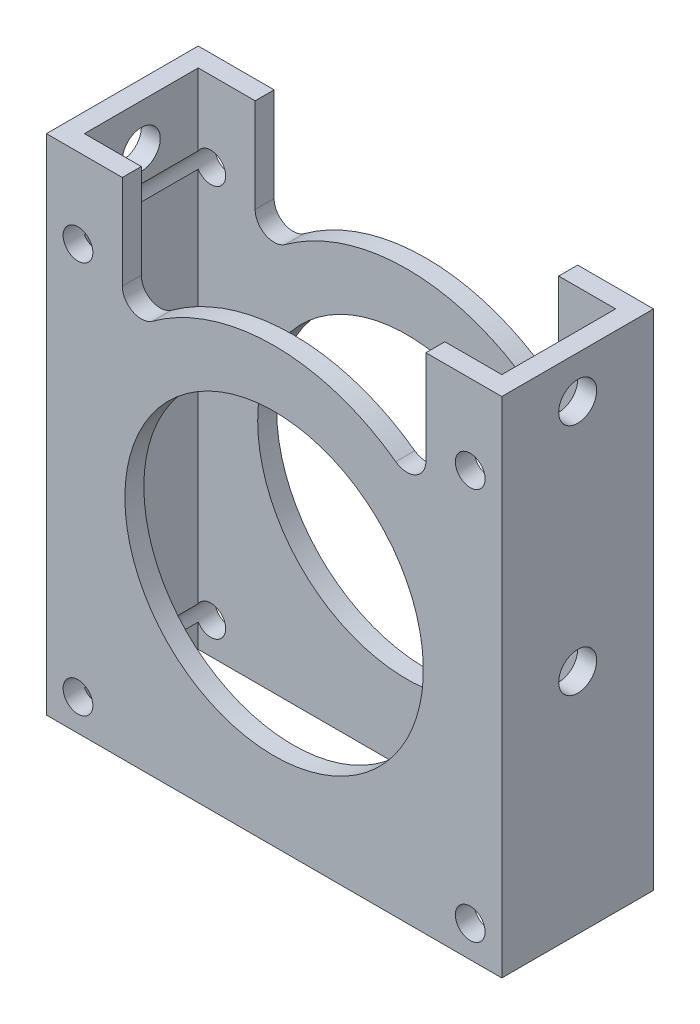
SolidWorks part; units mm, degrees
ref_plane "Front Plane" through (0, 0, 0) normal (0, 0, 1) x (1, 0, 0)
ref_plane "Top Plane" through (0, 0, 0) normal (0, 1, 0) x (1, 0, 0)
ref_plane "Right Plane" through (0, 0, 0) normal (1, 0, 0) x (0, 0, -1)
sketch "Sketch1" plane through (0, 0, 0) normal (0, 1, 0) x (1, 0, 0)
  line L1 (0, 0) -> (76.2, 0)
  line L2 (0, 0) -> (0, 25.4)
  line L3 (0, 25.4) -> (76.2, 25.4)
  line L4 (76.2, 0) -> (76.2, 25.4)
  dimension "D1" = 76.2
  dimension "D2" = 25.4
extrude "Extrude-Thin1" add sketch "Sketch1" along normal mid plane 98.552 thin thin type one direction reverse wall 3.175
sketch "Sketch2" plane through (0, 0, -25.4) normal (0, 0, -1) x (-1, 0, 0)
  line L7 (0, -49.276) -> (-76.2, 26.924) construction
  line L8 (-76.2, 49.276) -> (-76.2, -49.276) construction
  line L9 (0, 49.276) -> (0, -49.276) construction
  line L10 (-76.2, -49.276) -> (0, 26.924) construction
  circle A0 centre (-5.2832, 21.6408) radius 2.4892
  circle A2 centre (-38.1, -11.176) radius 24.972
  circle A3 centre (-70.9168, -43.9928) radius 2.4892
  point P14 (-2.794, 21.6408)
  point P17 (-73.406, -43.9928)
  dimension "D1" = 2.794
  dimension "D2" = 4.9784
  dimension "D3" = 49.944
  dimension "D4" = 2.794
extrude "Cut-Extrude1" cut sketch "Sketch2" against normal blind 52.578
sketch "Sketch5" plane through (0, 0, -25.4) normal (0, 0, -1) x (-1, 0, 0)
  line L0 (0, 49.276) -> (0, -49.276) construction
  line L1 (-76.2, 49.276) -> (0, 49.276)
  line L2 (-76.2, 49.276) -> (-76.2, 34.9885)
  line L3 (-76.2, 34.9885) -> (0, 34.9885)
  line L4 (0, 49.276) -> (0, 34.9885)
  line L6 (-63.5, 34.9885) -> (-12.7, 34.9885)
  line L7 (-63.5, 34.9885) -> (-63.5, 12.1667)
  line L8 (-63.5, 12.1667) -> (-12.7, 12.1667)
  line L9 (-12.7, 34.9885) -> (-12.7, 12.1667)
  circle A0 centre (-38.1, -11.176) radius 34.497
  arc A1 (-58.4519, 16.678) -> (-63.5, 19.2416) centre (-60.325, 19.2416) cw
  arc A2 (-17.7481, 16.678) -> (-12.7, 19.2416) centre (-15.875, 19.2416) ccw
  circle A5 centre (-38.1, -11.176) radius 24.972 construction
  point P21 (-38.1, 23.321)
  point P22 (-38.1, 17.0662)
  point P23 (-12.7, 12.1667)
  line M14 (0, -49.276) -> (0, 49.276)
  line M15 (0, 49.276) -> (-76.2, 49.276)
  line M16 (-76.2, 49.276) -> (-76.2, -49.276)
  dimension "D5" = 3.175
  dimension "D4" = 12.7
  dimension "D6" = 14.2875
  dimension "D1" = 12.7
  dimension "D2" = 9.525
extrude "Cut-Extrude2" cut sketch "Sketch5" against normal through all contours L3 M16 M14 M15 | A0 A2 L9 L3 L7 A1
sketch "Sketch6" plane through (0, 0, 0) normal (-1, 0, 0) x (0, 0, 1)
  line L0 (-12.7, 34.9885) -> (-12.7, 27.94) construction
  line L1 (0, 34.9885) -> (-25.4, 34.9885) construction
  line L2 (-25.4, -36.148) -> (-25.4, 13.796) construction
  line L3 (-25.4, 34.9885) -> (-25.4, -49.276) construction
  circle A0 centre (-12.7, 27.94) radius 3.175
  point P9 (-25.4, -11.176)
  dimension "D1" = 6.35
  dimension "D2" = 39.116
extrude "Cut-Extrude3" cut sketch "Sketch6" against normal through all
ref_plane "Plane2" through (38.1, 0, 0) normal (-1, 0, 0) x (0, 0, 1)
mirror "Mirror1" about plane through (38.1, 0, 0) normal (-1, 0, 0) of "Cut-Extrude1"
sketch "Sketch7" plane through (0, 0, 0) normal (-1, 0, 0) x (0, 0, 1)
  line L0 (-12.7, -49.276) -> (-12.7, -11.176) construction
  line L1 (-25.4, -49.276) -> (0, -49.276) construction
  line L2 (-25.4, 13.796) -> (-25.4, -36.148) construction
  line L3 (-25.4, 13.796) -> (-25.4, -36.148) construction
  line L4 (-25.4, -11.176) -> (-12.7, -11.176) construction
  circle A0 centre (-12.7, -11.176) radius 3.175
  dimension "D2" = 6.35
extrude "Cut-Extrude4" cut sketch "Sketch7" against normal through all
equation "\"D4@Sketch5\"=\"D1@Sketch5\""
